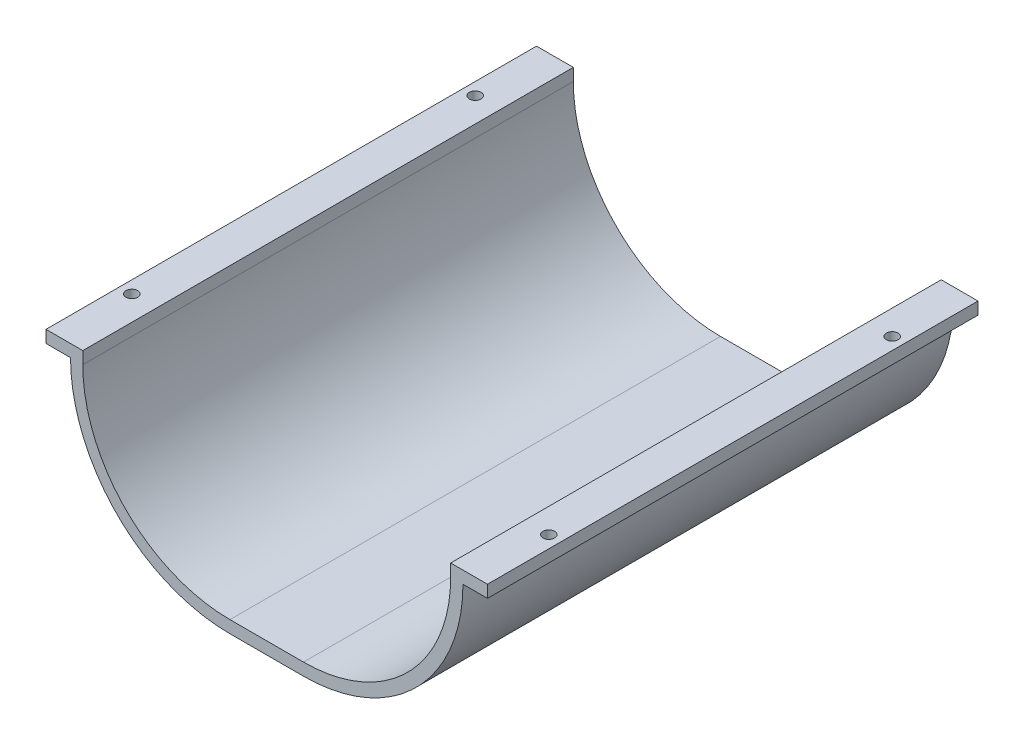
SolidWorks part; units mm, degrees
ref_plane "Front Plane" through (0, 0, 0) normal (0, 0, 1) x (1, 0, 0)
ref_plane "Top Plane" through (0, 0, 0) normal (0, 1, 0) x (1, 0, 0)
ref_plane "Right Plane" through (0, 0, 0) normal (1, 0, 0) x (0, 0, -1)
sketch "Sketch1" plane through (0, 0, 0) normal (0, 0, 1) x (1, 0, 0)
  line L1 (60, 0) -> (90, 0)
  line L2 (0, 60) -> (0, 65)
  line L4 (150, 60) -> (150, 65)
  line L5 (-5, 60) -> (-5, 65)
  line L6 (60, -5) -> (90, -5)
  line L7 (155, 60) -> (155, 65)
  line L8 (-5, 65) -> (155, 65)
  line L10 (-5, 60) -> (-15, 60)
  line L11 (-5, 60) -> (-5, 65)
  line L12 (-5, 65) -> (-15, 65)
  line L13 (-15, 60) -> (-15, 65)
  line L14 (155, 60) -> (165, 60)
  line L15 (155, 60) -> (155, 65)
  line L16 (155, 65) -> (165, 65)
  line L17 (165, 60) -> (165, 65)
  arc A0 (90, 0) -> (150, 60) centre (90, 60) ccw
  arc A1 (60, 0) -> (0, 60) centre (60, 60) cw
  arc A2 (60, -5) -> (-5, 60) centre (60, 60) cw
  arc A3 (90, -5) -> (155, 60) centre (90, 60) ccw
  point P12 (0, 0)
  dimension "D4" = 60
  dimension "D1" = 5
  dimension "D2" = 10
  dimension "D3" = 10
extrude "Boss-Extrude1" add sketch "Sketch1" along normal blind 200 contours L13 L10 L5 L12 | L6 A3 L7 L8 L4 A0 L1 A1 L2 L5 A2 | L14 L17 L16 L7
sketch "Sketch2" plane through (0, 65, 0) normal (0, 1, 0) x (1, 0, 0)
  line L0 (0, 0) -> (-15, 0) construction
  line L1 (-15, -200) -> (-5, -200)
  line L2 (-15, -200) -> (-15, 0)
  line L3 (-15, 0) -> (-5, 0)
  line L4 (-5, -200) -> (-5, 0)
  line L5 (150, -200) -> (165, -200) construction
  line L6 (165, 0) -> (155, 0)
  line L7 (165, 0) -> (165, -200)
  line L8 (165, -200) -> (155, -200)
  line L9 (155, 0) -> (155, -200)
  line L10 (160, -200) -> (160, 0)
  line L11 (160, 0) -> (-10, 0)
  line L12 (-10, 0) -> (-10, -200)
  circle A0 centre (-10, -170) radius 2.3813
  circle A1 centre (-10, -30) radius 2.3813
  circle A2 centre (160, -30) radius 2.3813
  circle A3 centre (160, -170) radius 2.3813
  dimension "D3" = 4.7625
  dimension "D4" = 4.7625
  dimension "D5" = 4.7625
  dimension "D6" = 4.7625
  dimension "D1" = 10
  dimension "D2" = 10
  dimension "D7" = 30
  dimension "D8" = 30
  dimension "D9" = 30
  dimension "D10" = 30
extrude "Cut-Extrude1" cut sketch "Sketch2" against normal blind 200 contours A1 | A0 | A3 | A2
